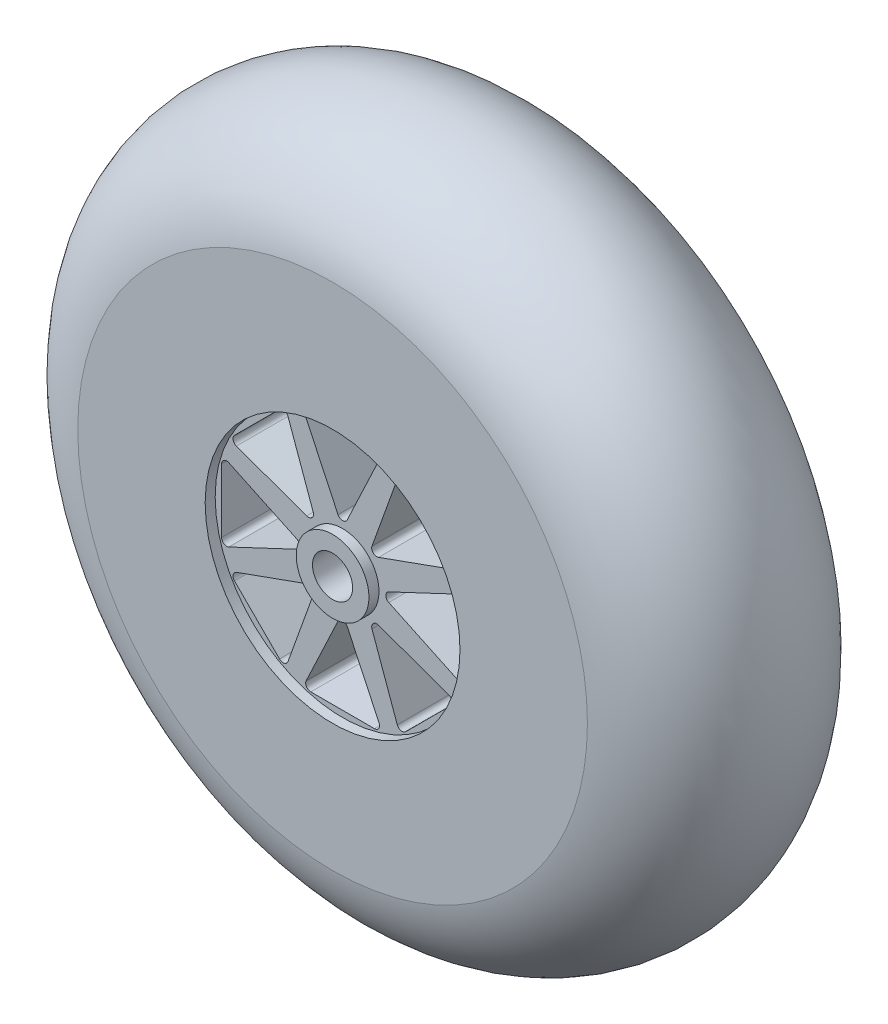
SolidWorks part; units mm, degrees
material "Rubber"
ref_plane "Front Plane" through (0, 0, 0) normal (0, 0, 1) x (1, 0, 0)
ref_plane "Top Plane" through (0, 0, 0) normal (0, 1, 0) x (1, 0, 0)
ref_plane "Right Plane" through (0, 0, 0) normal (1, 0, 0) x (0, 0, -1)
sketch "Sketch1" plane through (0, 0, 0) normal (1, 0, 0) x (0, 0, -1)
  line L0 (0, 25.4) -> (0, 2)
  line L1 (22.225, 25.4) -> (22.225, 2)
  line L2 (11.1125, 34.925) -> (11.1125, 0) construction
  line L3 (22.225, 0) -> (0, 0) construction
  line L4 (22.225, 2) -> (0, 2)
  arc A0 (0, 25.4) -> (22.225, 25.4) centre (11.1125, 23.6802) cw
  dimension "D3" = 34.925
  dimension "D1" = 25.4
  dimension "D2" = 22.225
  dimension "D4" = 2
revolve "Revolve1" add sketch "Sketch1" angle 360 about L3
sketch "Sketch2" plane through (0, 0, 0) normal (0, 0, 1) x (1, 0, 0)
  circle A0 centre (0, 0) radius 12.7
  circle A1 centre (0, 0) radius 3.625
  dimension "D1" = 25.4
  dimension "D2" = 7.25
extrude "Cut-Extrude1" cut sketch "Sketch2" against normal blind 1
sketch "Sketch3" plane through (0, 0, -1) normal (0, 0, 1) x (1, 0, 0)
  line L0 (0, 12.7) -> (0, 3.625) construction
  line L1 (-0.4595, 4.6001) -> (-3.6345, 11.337)
  line L2 (-3.175, 12.0616) -> (3.175, 12.0616)
  line L3 (0.4595, 4.6001) -> (3.6345, 11.337)
  line L4 (3.5777, 2.9278) -> (10.5865, 5.4465)
  line L5 (6.2838, 10.7739) -> (10.7739, 6.2838)
  line L6 (2.9278, 3.5777) -> (5.4465, 10.5865)
  line L7 (4.6001, -0.4595) -> (11.337, -3.6345)
  line L8 (12.0616, 3.175) -> (12.0616, -3.175)
  line L9 (4.6001, 0.4595) -> (11.337, 3.6345)
  line L10 (2.9278, -3.5777) -> (5.4465, -10.5865)
  line L11 (10.7739, -6.2838) -> (6.2838, -10.7739)
  line L12 (3.5777, -2.9278) -> (10.5865, -5.4465)
  line L13 (-0.4595, -4.6001) -> (-3.6345, -11.337)
  line L14 (3.175, -12.0616) -> (-3.175, -12.0616)
  line L15 (0.4595, -4.6001) -> (3.6345, -11.337)
  line L16 (-3.5777, -2.9278) -> (-10.5865, -5.4465)
  line L17 (-6.2838, -10.7739) -> (-10.7739, -6.2838)
  line L18 (-2.9278, -3.5777) -> (-5.4465, -10.5865)
  line L19 (-4.6001, 0.4595) -> (-11.337, 3.6345)
  line L20 (-12.0616, -3.175) -> (-12.0616, 3.175)
  line L21 (-4.6001, -0.4595) -> (-11.337, -3.6345)
  line L22 (-2.9278, 3.5777) -> (-5.4465, 10.5865)
  line L23 (-10.7739, 6.2838) -> (-6.2838, 10.7739)
  line L24 (-3.5777, 2.9278) -> (-10.5865, 5.4465)
  circle A0 centre (0, 0) radius 12.7 construction
  circle A1 centre (0, 0) radius 12.7 construction
  circle A2 centre (0, 0) radius 3.625 construction
  arc A3 (-3.175, 12.0616) -> (-3.6345, 11.337) centre (-3.175, 11.5536) ccw
  arc A4 (3.175, 12.0616) -> (3.6345, 11.337) centre (3.175, 11.5536) cw
  arc A5 (0.4595, 4.6001) -> (-0.4595, 4.6001) centre (0, 4.8166) cw
  arc A6 (3.5777, 2.9278) -> (2.9278, 3.5777) centre (3.4059, 3.4059) cw
  arc A7 (10.7739, 6.2838) -> (10.5865, 5.4465) centre (10.4147, 5.9245) cw
  arc A8 (6.2838, 10.7739) -> (5.4465, 10.5865) centre (5.9245, 10.4147) ccw
  arc A9 (4.6001, -0.4595) -> (4.6001, 0.4595) centre (4.8166, 0) cw
  arc A10 (12.0616, -3.175) -> (11.337, -3.6345) centre (11.5536, -3.175) cw
  arc A11 (12.0616, 3.175) -> (11.337, 3.6345) centre (11.5536, 3.175) ccw
  arc A12 (2.9278, -3.5777) -> (3.5777, -2.9278) centre (3.4059, -3.4059) cw
  arc A13 (6.2838, -10.7739) -> (5.4465, -10.5865) centre (5.9245, -10.4147) cw
  arc A14 (10.7739, -6.2838) -> (10.5865, -5.4465) centre (10.4147, -5.9245) ccw
  arc A15 (-0.4595, -4.6001) -> (0.4595, -4.6001) centre (0, -4.8166) cw
  arc A16 (-3.175, -12.0616) -> (-3.6345, -11.337) centre (-3.175, -11.5536) cw
  arc A17 (3.175, -12.0616) -> (3.6345, -11.337) centre (3.175, -11.5536) ccw
  arc A18 (-3.5777, -2.9278) -> (-2.9278, -3.5777) centre (-3.4059, -3.4059) cw
  arc A19 (-10.7739, -6.2838) -> (-10.5865, -5.4465) centre (-10.4147, -5.9245) cw
  arc A20 (-6.2838, -10.7739) -> (-5.4465, -10.5865) centre (-5.9245, -10.4147) ccw
  arc A21 (-4.6001, 0.4595) -> (-4.6001, -0.4595) centre (-4.8166, 0) cw
  arc A22 (-12.0616, 3.175) -> (-11.337, 3.6345) centre (-11.5536, 3.175) cw
  arc A23 (-12.0616, -3.175) -> (-11.337, -3.6345) centre (-11.5536, -3.175) ccw
  arc A24 (-2.9278, 3.5777) -> (-3.5777, 2.9278) centre (-3.4059, 3.4059) cw
  arc A25 (-6.2838, 10.7739) -> (-5.4465, 10.5865) centre (-5.9245, 10.4147) cw
  arc A26 (-10.7739, 6.2838) -> (-10.5865, 5.4465) centre (-10.4147, 5.9245) ccw
  point P14 (-3.976, 12.0616)
  point P18 (0, 12.0616)
  point P86 (0, 0)
  dimension "D1" = 0.508
  dimension "D2" = 0.508
  dimension "D3" = 6.35
  dimension "D4" = 8
extrude "Cut-Extrude2" cut sketch "Sketch3" against normal blind 9.525
